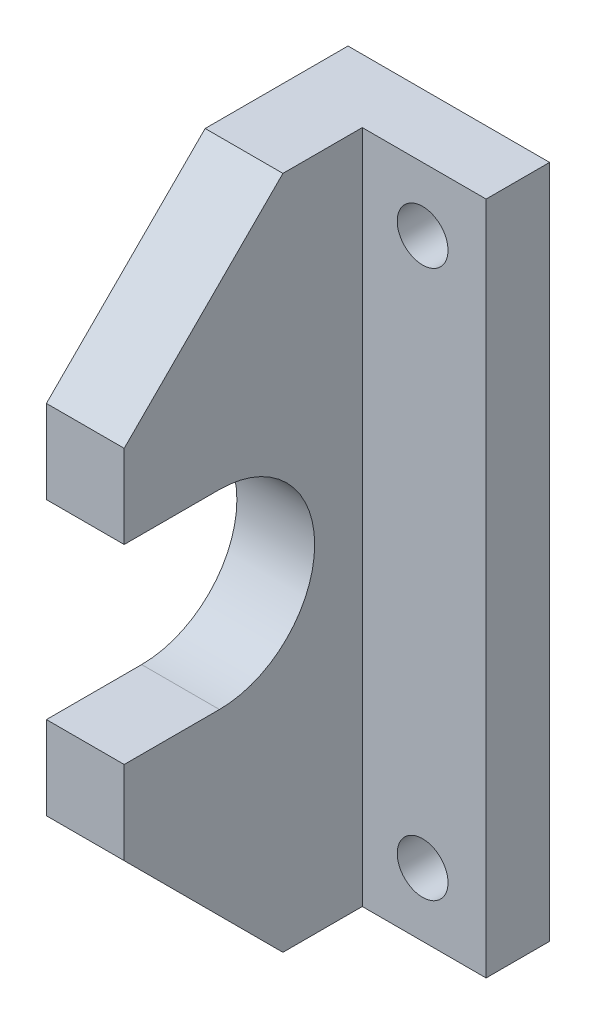
SolidWorks part; units mm, degrees
ref_plane "Plan de face" through (0, 0, 0) normal (0, 0, 1) x (1, 0, 0)
ref_plane "Plan de dessus" through (0, 0, 0) normal (0, 1, 0) x (1, 0, 0)
ref_plane "Plan de droite" through (0, 0, 0) normal (1, 0, 0) x (0, 0, -1)
sketch "Esquisse1" plane through (0, 0, 0) normal (0, 0, 1) x (1, 0, 0)
  line L0 (-1.3845, 0) -> (38.6155, 0) construction
  line L1 (38.6155, 42.5) -> (25.9155, 42.5)
  line L2 (38.6155, 42.5) -> (38.6155, 0)
  line L3 (38.6155, 0) -> (25.9155, 0)
  line L4 (25.9155, 42.5) -> (25.9155, 0)
  circle A0 centre (34.6155, 4) radius 1.6 construction
  circle A1 centre (34.6155, 4) radius 1.6
  circle A2 centre (34.6155, 38.5) radius 1.6 construction
  circle A3 centre (34.6155, 38.5) radius 1.6
  dimension "D1" = 12.7
extrude "Boss.-Extru.1" add sketch "Esquisse1" along normal blind 4
sketch "Esquisse2" plane through (0, 0, 4) normal (0, 0, 1) x (1, 0, 0)
  line L0 (25.9155, 0) -> (38.6155, 0) construction
  line L1 (25.9155, 42.5) -> (30.8155, 42.5)
  line L2 (25.9155, 42.5) -> (25.9155, 0)
  line L3 (25.9155, 0) -> (30.8155, 0)
  line L4 (30.8155, 42.5) -> (30.8155, 0)
  dimension "D1" = 4.9
extrude "Boss.-Extru.2" add sketch "Esquisse2" along normal blind 15
sketch "Esquisse3" plane through (30.8155, 0, 0) normal (1, 0, 0) x (0, 0, -1)
  line L0 (-19, 21.25) -> (-4, 21.25) construction
  line L1 (-19, 0) -> (-19, 42.5) construction
  line L2 (-4, 0) -> (-4, 42.5) construction
  line L3 (-13, 27.25) -> (-19, 27.25)
  line L4 (-19, 27.25) -> (-19, 15.25)
  line L5 (-19, 15.25) -> (-13, 15.25)
  arc A0 (-13, 15.25) -> (-13, 27.25) centre (-13, 21.25) ccw
  dimension "D1" = 12
  dimension "D2" = 9
extrude "Enlèv. mat.-Extru.1" cut sketch "Esquisse3" against normal through all
sketch "Esquisse4" plane through (38.6155, 0, 0) normal (1, 0, 0) x (0, 0, -1)
  line L4 (0, 0) -> (0, 42.5)
  line L5 (0, 42.5) -> (-4, 42.5)
  line L6 (-4, 42.5) -> (-4, 0)
  line L7 (-4, 0) -> (0, 0)
  line L8 (0, 0) -> (0, 42.5)
  line L9 (0, 42.5) -> (-4, 42.5)
  line L10 (-4, 42.5) -> (-4, 0)
  line L11 (-4, 0) -> (0, 0)
  dimension "D1" = 0
chamfer "Chanfrein1" distance 10 angle 45 2 edges at (28.3655, 42.5, 19) (28.3655, 0, 19)
